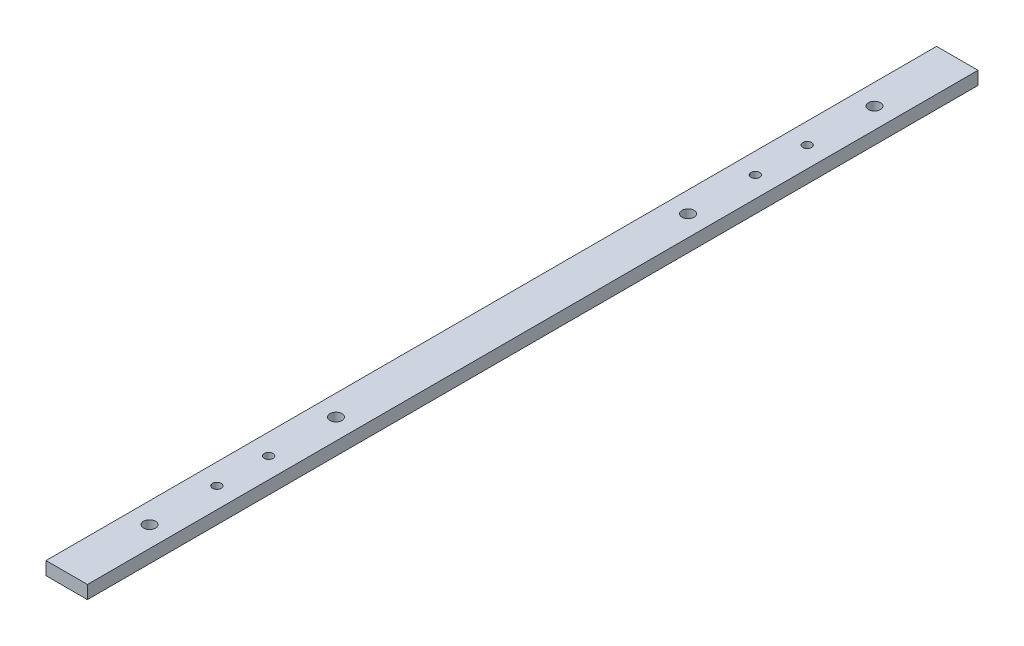
SolidWorks part; units mm, degrees
ref_plane "Front Plane" through (0, 0, 0) normal (0, 0, 1) x (1, 0, 0)
ref_plane "Top Plane" through (0, 0, 0) normal (0, 1, 0) x (1, 0, 0)
ref_plane "Right Plane" through (0, 0, 0) normal (1, 0, 0) x (0, 0, -1)
sketch "Sketch1" plane through (0, 0, 0) normal (0, 1, 0) x (1, 0, 0)
  line L1 (-10, -215) -> (10, -215)
  line L2 (-10, -215) -> (-10, 215)
  line L3 (-10, 215) -> (10, 215)
  line L4 (10, -215) -> (10, 215)
  line L5 (-10, -215) -> (10, 215) construction
  line L6 (-10, 215) -> (10, -215) construction
  point P0 (0, 0)
  dimension "D1" = 20
  dimension "D2" = 430
extrude "Boss-Extrude1" add sketch "Sketch1" along normal blind 6.35
hole_wizard "M5 Clearance Hole1" positions "Sketch2" profile "Sketch3" hole size "M5" standard "ANSI Metric" end condition through all
sketch "Sketch2" plane through (0, 6.35, 0) normal (0, 1, 0) x (1, 0, 0)
  line L0 (-10, -215) -> (10, -215) construction
  point P0 (0, -175)
  point P2 (0, -85)
  dimension "D1" = 40
  dimension "D2" = 90
sketch "Sketch3" plane through (0, 6.35, 175) normal (1, 0, 0) x (0, 0, 1)
  line L0 (0, 0) -> (0, 6.35)
  line L1 (0, 6.35) -> (2.9, 6.35)
  line L2 (2.9, 6.35) -> (2.9, 0)
  line L5 (2.9, 0) -> (0, 0)
  line L11 (0, -6.35) -> (0, 107.95) construction
  dimension "Thru Hole Dia." = 5.8
  dimension "Thru Hole Depth" = 6.35
mirror "Mirror1" about plane through (0, 0, 0) normal (0, 0, 1) of "M5 Clearance Hole1"
hole_wizard "M5x0.8 Tapped Hole1" positions "Sketch4" profile "Sketch5" tap size "M5x0.8" standard "ANSI Metric" end condition through all
sketch "Sketch4" plane through (0, 6.35, 0) normal (0, 1, 0) x (1, 0, 0)
  line L5 (0, -175) -> (0, -142.5) construction
  line L7 (0, -117.5) -> (0, -85) construction
  point P0 (0, -142.5)
  point P2 (0, -117.5)
  dimension "D1" = 25
sketch "Sketch5" plane through (0, 6.35, 142.5) normal (1, 0, 0) x (0, 0, 1)
  line L0 (0, 0) -> (0, 6.35)
  line L1 (0, 6.35) -> (2.1, 6.35)
  line L2 (2.1, 6.35) -> (2.1, 0)
  line L5 (2.1, 0) -> (0, 0)
  line L11 (0, -6.35) -> (0, 107.95) construction
  dimension "Thru Tap Drill Dia." = 4.2
  dimension "Thru Tap Drill Depth" = 6.35
cosmetic thread "Hole Thread1" parameters "D2"=5
cosmetic thread "Hole Thread2" parameters "D2"=5
mirror "Mirror2" about plane through (0, 0, 0) normal (0, 0, 1) of "M5x0.8 Tapped Hole1"
